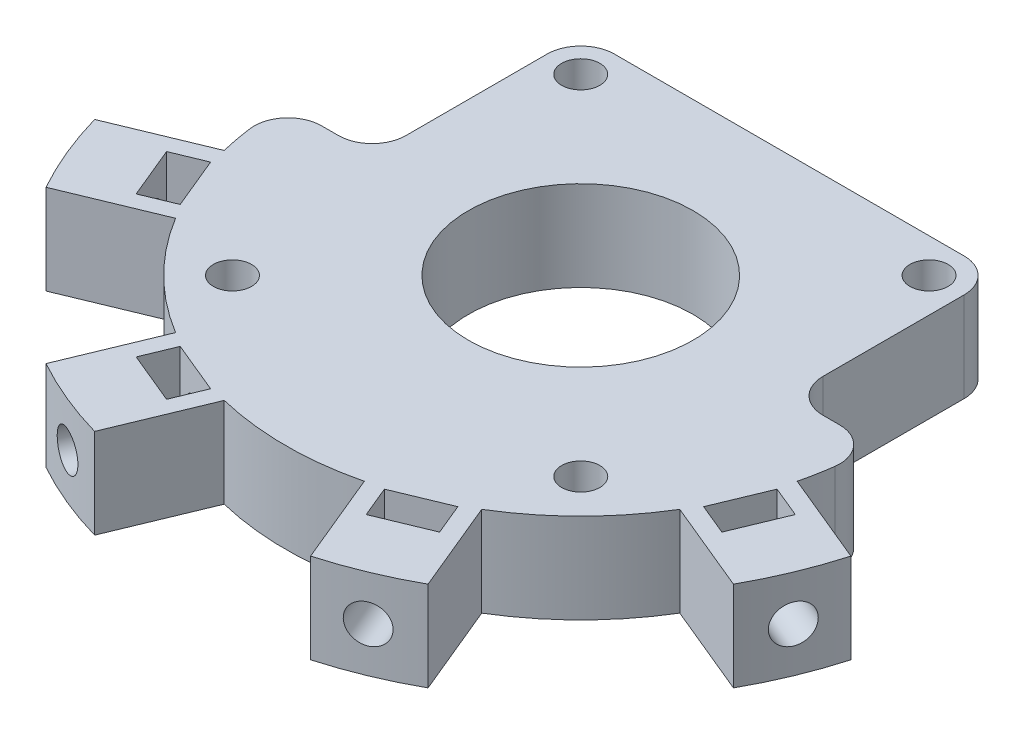
SolidWorks part; units mm, degrees
ref_plane "Alzado" through (0, 0, 0) normal (0, 0, 1) x (1, 0, 0)
ref_plane "Planta" through (0, 0, 0) normal (0, 1, 0) x (1, 0, 0)
ref_plane "Vista lateral" through (0, 0, 0) normal (1, 0, 0) x (0, 0, -1)
sketch "Croquis1" plane through (0, 0, 0) normal (0, 1, 0) x (1, 0, 0)
  line L0 (0, 0) -> (-28.0346, 0) construction
  line L1 (0, 0) -> (-32.3358, -13.3939) construction
  line L2 (-33.6547, -9.6106) -> (-25.4994, -6.2326)
  line L4 (-15.5, 15.5) -> (15.5, 15.5) construction
  line L5 (-15.5, 15.5) -> (-15.5, -15.5) construction
  line L6 (-15.5, -15.5) -> (15.5, -15.5) construction
  line L7 (15.5, 15.5) -> (15.5, -15.5) construction
  line L8 (-15.5, 15.5) -> (15.5, -15.5) construction
  line L9 (-15.5, -15.5) -> (15.5, 15.5) construction
  line L13 (-30.5932, -17.0017) -> (-22.4379, -13.6236)
  line L15 (-9.6106, -33.6547) -> (-6.2326, -25.4994)
  line L16 (-17.0017, -30.5932) -> (-13.6236, -22.4379)
  line L17 (17.0017, -30.5932) -> (13.6236, -22.4379)
  line L18 (9.6106, -33.6547) -> (6.2326, -25.4994)
  line L19 (33.6547, -9.6106) -> (25.4994, -6.2326)
  line L20 (30.5932, -17.0017) -> (22.4379, -13.6236)
  circle A0 centre (0, 0) radius 35 construction
  arc A1 (-33.6547, -9.6106) -> (-30.5932, -17.0017) centre (0, 0) ccw
  arc A2 (-22.4379, -13.6236) -> (-13.6236, -22.4379) centre (0, 0) ccw
  arc A3 (-17.0017, -30.5932) -> (-9.6106, -33.6547) centre (0, 0) ccw
  arc A4 (9.6106, -33.6547) -> (17.0017, -30.5932) centre (0, 0) ccw
  arc A5 (30.5932, -17.0017) -> (33.6547, -9.6106) centre (0, 0) ccw
  arc A6 (-6.2326, -25.4994) -> (6.2326, -25.4994) centre (0, 0) ccw
  arc A7 (13.6236, -22.4379) -> (22.4379, -13.6236) centre (0, 0) ccw
  arc A8 (25.4994, -6.2326) -> (-25.4994, -6.2326) centre (0, 0) ccw
  point P7 (-18.5, 18.5)
  point P14 (-18.5, -18.5)
  point P31 (0, 0)
  dimension "D1" = 70
  dimension "D5" = 52.5
  dimension "D2" = 22.5
  dimension "D3" = 8
  dimension "D4" = 31
  dimension "D6" = 4
extrude "Saliente-Extruir1" add sketch "Croquis1" along normal blind 8
ref_plane "Plano1" through (-32.3358, 0, 13.3939) normal (-0.9239, 0, 0.3827) x (0.3827, 0, 0.9239)
sketch "Croquis3" plane through (-32.3358, 0, 13.3939) normal (-0.9239, 0, 0.3827) x (0.3827, 0, 0.9239)
  circle A1 centre (0, 4) radius 1.7
  dimension "D1" = 3.4
extrude "Cortar-Extruir1" cut sketch "Croquis3" against normal blind 10
sketch "Croquis4" plane through (0, 8, 0) normal (0, 1, 0) x (1, 0, 0)
  line L0 (-32.3358, -13.3939) -> (-19.2088, -7.9566) construction
  line L1 (-27.9802, -8.8838) -> (-26.0668, -13.5032)
  line L2 (-26.0668, -13.5032) -> (-23.2951, -12.3551)
  line L3 (-23.2951, -12.3551) -> (-25.2085, -7.7357)
  line L4 (-25.2085, -7.7357) -> (-27.9802, -8.8838)
  arc A0 (-33.6547, -9.6106) -> (-30.5932, -17.0017) centre (0, 0) ccw construction
  arc A1 (25.4994, -6.2326) -> (-25.4994, -6.2326) centre (0, 0) ccw construction
  point P9 (-27.0235, -11.1935)
  dimension "D1" = 5
  dimension "D2" = 3
extrude "Cortar-Extruir2" cut sketch "Croquis4" against normal blind 7
pattern_circular "MatrizC1" count 4 over 135 about axis through (0, 0, 0) along (0, 1, 0) of "Cortar-Extruir1", "Cortar-Extruir2"
sketch "Croquis5" plane through (0, 8, 0) normal (0, 1, 0) x (1, 0, 0)
  line L1 (-15.5, 15.5) -> (15.5, 15.5) construction
  line L2 (-15.5, 15.5) -> (-15.5, -15.5) construction
  line L3 (-15.5, -15.5) -> (15.5, -15.5) construction
  line L4 (15.5, 15.5) -> (15.5, -15.5) construction
  line L5 (-15.5, 15.5) -> (15.5, -15.5) construction
  line L6 (-15.5, -15.5) -> (15.5, 15.5) construction
  circle A0 centre (0, 0) radius 10
  circle A1 centre (-15.5, 15.5) radius 1.7
  circle A2 centre (15.5, 15.5) radius 1.7
  circle A3 centre (15.5, -15.5) radius 1.7
  circle A4 centre (-15.5, -15.5) radius 1.7
  point P17 (0, 0)
  dimension "D1" = 20
  dimension "D3" = 3.4
  dimension "D2" = 31
  dimension "D4" = 4
extrude "Cortar-Extruir3" cut sketch "Croquis5" against normal up to surface (8 mm away) up to face at (0, 0, 17.9523)
sketch "Croquis6" plane through (0, 8, 0) normal (0, 1, 0) x (1, 0, 0)
  line L0 (-15.5, 15.5) -> (-18.5616, 18.5616) construction
  line L1 (15.5, 15.5) -> (18.5616, 18.5616) construction
  line L2 (18.5616, 18.5616) -> (-18.5616, 18.5616)
  line L3 (-18.5616, 18.5616) -> (-18.5616, 0)
  line L4 (-18.5616, 0) -> (-26.25, 0)
  line L5 (-26.25, 0) -> (-26.25, 31.2881)
  line L6 (-26.25, 31.2881) -> (26.25, 31.2881)
  line L7 (26.25, 31.2881) -> (26.25, 0)
  line L8 (26.25, 0) -> (18.5616, 0)
  line L9 (18.5616, 0) -> (18.5616, 18.5616)
  arc A0 (25.4994, -6.2326) -> (-25.4994, -6.2326) centre (0, 0) ccw construction
extrude "Cortar-Extruir4" cut sketch "Croquis6" against normal up to surface (8 mm away) up to face at (-15.5, 0, 17.2)
fillet "Redondeo1" radius 3 6 edges at (26.25, 4, 0) (18.5616, 4, 0) (18.5616, 4, -18.5616) (-18.5616, 4, -18.5616) (-18.5616, 4, 0) (-26.25, 4, 0)
